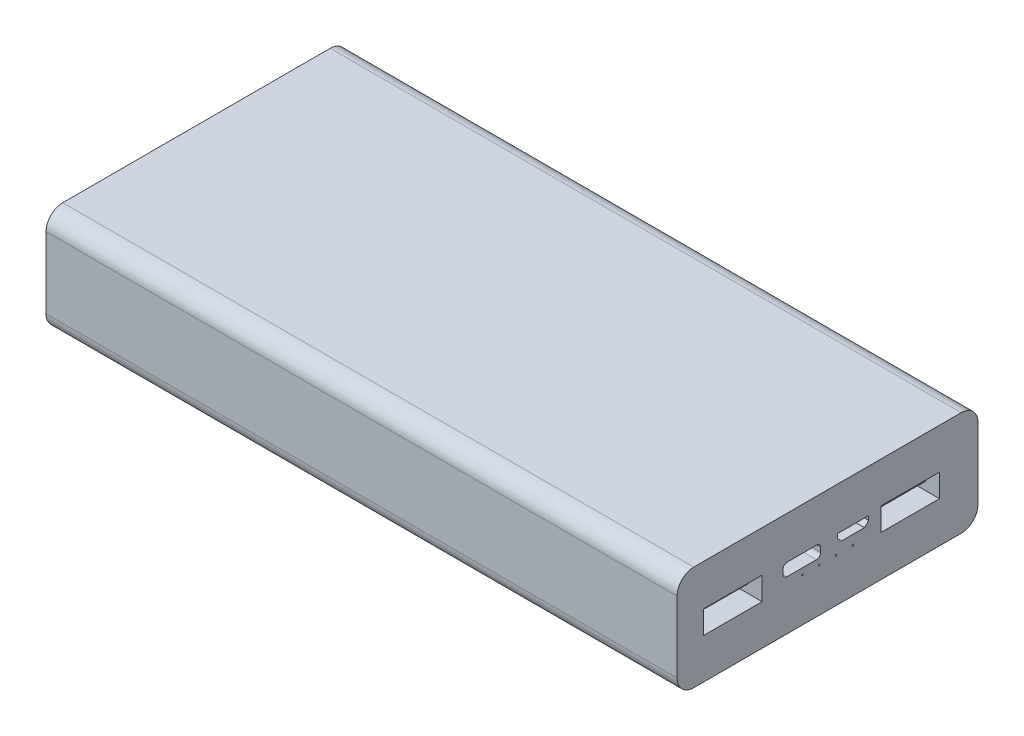
SolidWorks part; units mm, degrees
material "ABS"
ref_plane "Front" through (0, 0, 0) normal (0, 0, 1) x (1, 0, 0)
ref_plane "Top" through (0, 0, 0) normal (0, 1, 0) x (1, 0, 0)
ref_plane "Right" through (0, 0, 0) normal (1, 0, 0) x (0, 0, -1)
sketch "草图1" plane through (0, 0, 0) normal (0, 1, 0) x (1, 0, 0)
  line L1 (53.6854, -36.3817) -> (-97.3146, -36.3817)
  line L2 (53.6854, -36.3817) -> (53.6854, 35.6183)
  line L3 (53.6854, 35.6183) -> (-97.3146, 35.6183)
  line L4 (-97.3146, -36.3817) -> (-97.3146, 35.6183)
  dimension "D1" = 151
  dimension "D2" = 72
extrude "凸台-拉伸1" add sketch "草图1" along normal blind 25
fillet "圆角1" radius 4 1 edges at (-21.8146, 25, 36.3817)
fillet "圆角2" radius 4 1 edges at (-21.8146, 25, -35.6183)
fillet "圆角3" radius 4 1 edges at (-21.8146, 0, 36.3817)
fillet "圆角4" radius 4 1 edges at (-21.8146, 0, -35.6183)
sketch "草图2" plane through (53.6854, 0, 0) normal (1, 0, 0) x (0, 0, -1)
  line L0 (-0.3817, 31.1144) -> (-0.3817, -2.5055) construction
  line L1 (-30.0329, 15.1581) -> (-16.0329, 15.1581)
  line L2 (-30.0329, 15.1581) -> (-30.0329, 9.6581)
  line L3 (-30.0329, 9.6581) -> (-16.0329, 9.6581)
  line L4 (-16.0329, 15.1581) -> (-16.0329, 9.6581)
  line L5 (-10.0329, 14.8548) -> (-3.0329, 14.8548)
  line L6 (-11.0329, 13.8548) -> (-11.0329, 12.8548)
  line L7 (-10.0329, 11.8548) -> (-3.0329, 11.8548)
  line L8 (-2.0329, 13.8548) -> (-2.0329, 12.8548)
  line L9 (1.9671, 14.7412) -> (9.4671, 14.7412)
  line L10 (1.9671, 14.7412) -> (1.9671, 13.7412)
  line L11 (2.9671, 12.7412) -> (8.4671, 12.7412)
  line L12 (9.4671, 14.7412) -> (9.4671, 13.7412)
  line L13 (12.4007, 15.2772) -> (26.4007, 15.2772)
  line L14 (12.4007, 15.2772) -> (12.4007, 9.7772)
  line L15 (12.4007, 9.7772) -> (26.4007, 9.7772)
  line L16 (26.4007, 15.2772) -> (26.4007, 9.7772)
  line L17 (-36.3817, 21) -> (-36.3817, 4) construction
  line L18 (35.6183, 21) -> (35.6183, 4) construction
  line L19 (40.6915, 12.5) -> (-43.5475, 12.5) construction
  line L20 (-32.3817, 25) -> (31.6183, 25) construction
  line L21 (-32.3817, 0) -> (31.6183, 0) construction
  line L22 (1.9671, 13.7412) -> (2.9671, 12.7412)
  line L23 (9.4671, 13.7412) -> (8.4671, 12.7412)
  arc A0 (-2.0329, 12.8548) -> (-3.0329, 11.8548) centre (-3.0329, 12.8548) cw
  arc A1 (-3.0329, 14.8548) -> (-2.0329, 13.8548) centre (-3.0329, 13.8548) cw
  arc A2 (-11.0329, 12.8548) -> (-10.0329, 11.8548) centre (-10.0329, 12.8548) ccw
  arc A3 (-11.0329, 13.8548) -> (-10.0329, 14.8548) centre (-10.0329, 13.8548) cw
  circle A4 centre (-6.3817, 10.439) radius 0.2
  circle A5 centre (-2.3817, 10.439) radius 0.2
  circle A6 centre (1.6183, 10.439) radius 0.2
  circle A7 centre (5.6183, 10.439) radius 0.2
  point P32 (-2.0329, 14.8548)
  point P35 (-11.0329, 11.8548)
  point P38 (-11.0329, 14.8548)
  dimension "D8" = 1
  dimension "D10" = 4
  dimension "D1" = 14
  dimension "D2" = 5.5
  dimension "D3" = 14
  dimension "D4" = 5.5
  dimension "D5" = 9
  dimension "D6" = 3
  dimension "D7" = 5
  dimension "D9" = 7.5
  dimension "D11" = 4
  dimension "D12" = 135
  dimension "D13" = 1
  dimension "D14" = 1
  dimension "D15" = 135
  dimension "D16" = 2
extrude "切除-拉伸1" cut sketch "草图2" against normal blind 15 contours L14 L15 L16 L13 | L2 L3 L4 L1 | L7 A0 L8 A1 L5 A3 L6 A2 | L11 L23 L12 L9 L10 L22 | A4 | A5 | A6 | A7
sketch "草图3" plane through (38.6854, 0, 0) normal (1, 0, 0) x (0, 0, -1)
  line L0 (-23.0329, 18.6783) -> (-23.0329, 7.2414) construction
  line L1 (-29.2196, 14.1359) -> (-16.8463, 14.1359)
  line L2 (-29.2196, 14.1359) -> (-29.2196, 12.5535)
  line L3 (-29.2196, 12.5535) -> (-16.8463, 12.5535)
  line L4 (-16.8463, 14.1359) -> (-16.8463, 12.5535)
  line L5 (13.2141, 14.1359) -> (25.5873, 14.1359)
  line L6 (13.2141, 14.1359) -> (13.2141, 12.5535)
  line L7 (13.2141, 12.5535) -> (25.5873, 12.5535)
  line L8 (25.5873, 14.1359) -> (25.5873, 12.5535)
  line L9 (19.4007, 18.6783) -> (19.4007, 6.637) construction
  line L10 (-16.0329, 15.1581) -> (-16.0329, 9.6581) construction
  line L12 (-30.0329, 15.1581) -> (-30.0329, 9.6581) construction
  line L13 (26.4007, 15.2772) -> (26.4007, 9.7772) construction
  line L14 (12.4007, 15.2772) -> (12.4007, 9.7772) construction
  line L15 (-6.5329, 15.8891) -> (-6.5329, 11.4136) construction
  line L16 (-10.0717, 13.4486) -> (-2.9942, 13.4486)
  line L17 (-10.0717, 13.4486) -> (-10.0717, 12.9486)
  line L18 (-10.0717, 12.9486) -> (-2.9942, 12.9486)
  line L19 (-2.9942, 13.4486) -> (-2.9942, 12.9486)
  line L20 (3.8127, 14.013) -> (7.6214, 14.013)
  line L21 (3.8127, 14.013) -> (3.8127, 13.813)
  line L22 (3.8127, 13.813) -> (7.6214, 13.813)
  line L23 (7.6214, 14.013) -> (7.6214, 13.813)
  line L24 (-11.0329, 13.8548) -> (-11.0329, 12.8548) construction
  line L25 (-2.0329, 13.8548) -> (-2.0329, 12.8548) construction
  line L26 (5.7171, 15.4512) -> (5.7171, 11.9019) construction
  line L27 (1.9671, 14.7412) -> (1.9671, 13.7412) construction
  line L28 (9.4671, 14.7412) -> (9.4671, 13.7412) construction
  dimension "D1" = 0.5
  dimension "D2" = 0.2
extrude "凸台-拉伸2" add sketch "草图3" along normal blind 13
chamfer "倒角1" distance 0.5 angle 45 1 edges at (51.6854, 12.5535, 23.0329)
chamfer "倒角2" distance 0.5 angle 45 1 edges at (51.6854, 14.1359, 23.0329)
chamfer "倒角3" distance 0.5 angle 45 1 edges at (51.6854, 13.3447, 29.2196)
chamfer "倒角4" distance 0.5 angle 45 1 edges at (51.6854, 13.3447, 16.8463)
chamfer "倒角5" distance 0.5 angle 45 4 edges at (51.6854, 13.3447, -13.2141) (51.6854, 14.1359, -19.4007) (51.6854, 13.3447, -25.5873) (51.6854, 12.5535, -19.4007)
sketch "草图4" plane through (0, 0, -35.6183) normal (0, 0, -1) x (-1, 0, 0)
  line L0 (-53.6854, 21) -> (-53.6854, 4) construction
  line L1 (-40.8854, 14.2739) -> (-30.4854, 14.2739)
  line L2 (-41.6854, 13.4739) -> (-41.6854, 10.3788)
  line L3 (-40.8854, 9.5788) -> (-30.4854, 9.5788)
  line L4 (-29.6854, 13.4739) -> (-29.6854, 10.3788)
  line L6 (-40.8854, 14.3239) -> (-30.4854, 14.3239)
  line L7 (-41.7354, 13.4739) -> (-41.7354, 10.3788)
  line L8 (-40.8854, 9.5288) -> (-30.4854, 9.5288)
  line L9 (-29.6354, 13.4739) -> (-29.6354, 10.3788)
  arc A0 (-30.4854, 14.2739) -> (-29.6854, 13.4739) centre (-30.4854, 13.4739) cw
  arc A1 (-30.4854, 9.5788) -> (-29.6854, 10.3788) centre (-30.4854, 10.3788) ccw
  arc A2 (-40.8854, 9.5788) -> (-41.6854, 10.3788) centre (-40.8854, 10.3788) cw
  arc A3 (-41.6854, 13.4739) -> (-40.8854, 14.2739) centre (-40.8854, 13.4739) cw
  arc A4 (-30.4854, 9.5288) -> (-29.6354, 10.3788) centre (-30.4854, 10.3788) ccw
  arc A5 (-29.6354, 13.4739) -> (-30.4854, 14.3239) centre (-30.4854, 13.4739) ccw
  arc A6 (-41.7354, 10.3788) -> (-40.8854, 9.5288) centre (-40.8854, 10.3788) ccw
  arc A7 (-41.7354, 13.4739) -> (-40.8854, 14.3239) centre (-40.8854, 13.4739) cw
  dimension "D1" = 0.8
  dimension "D2" = 0.8
  dimension "D10" = 0.85
  dimension "D3" = 12
  dimension "D4" = 4.6951
  dimension "D5" = 12
  dimension "D6" = 0.05
  dimension "D7" = 0.05
  dimension "D8" = 0.05
  dimension "D9" = 0.05
extrude "切除-拉伸2" cut sketch "草图4" against normal blind 3
sketch "草图5" plane through (0, 0, -35.6183) normal (0, 0, -1) x (-1, 0, 0)
  line L0 (-30.4854, 14.3239) -> (-40.8854, 14.3239) construction
  line L1 (-40.9354, 14.8239) -> (-30.4354, 14.8239)
  line L2 (-42.2354, 13.5239) -> (-42.2354, 10.3288)
  line L3 (-40.9354, 9.0288) -> (-30.4354, 9.0288)
  line L4 (-29.1354, 13.5239) -> (-29.1354, 10.3288)
  line L5 (-29.6354, 10.3788) -> (-29.6354, 13.4739) construction
  line L6 (-40.8854, 9.5288) -> (-30.4854, 9.5288) construction
  line L7 (-41.7354, 13.4739) -> (-41.7354, 10.3788) construction
  arc A0 (-40.9354, 9.0288) -> (-42.2354, 10.3288) centre (-40.9354, 10.3288) cw
  arc A1 (-30.4354, 9.0288) -> (-29.1354, 10.3288) centre (-30.4354, 10.3288) ccw
  arc A2 (-30.4354, 14.8239) -> (-29.1354, 13.5239) centre (-30.4354, 13.5239) cw
  arc A3 (-40.9354, 14.8239) -> (-42.2354, 13.5239) centre (-40.9354, 13.5239) ccw
  dimension "D5" = 1.3
  dimension "D1" = 0.5
  dimension "D2" = 0.5
  dimension "D3" = 0.5
  dimension "D4" = 0.5
ref_plane "基准面1" through (0, 11, 0) normal (0, 1, 0) x (1, 0, 0)
sketch "草图6" plane through (0, 11, 0) normal (0, 1, 0) x (1, 0, 0)
  line L1 (41.7354, 35.5168) -> (41.7354, 35.6183)
  line L2 (41.7354, 35.6183) -> (42.2354, 35.6183)
  line L3 (30.4854, 35.6183) -> (29.6354, 35.6183) construction
  line L4 (42.2354, 35.6183) -> (42.1849, 35.5157) construction
  line L5 (42.1849, 35.5157) -> (41.7354, 35.5168) construction
  spline S0 degree 2 poles (42.2354, 35.6183) (42.1849, 35.5157) (41.7354, 35.5168) knots 0 0 0 1 1 1
sweep "切除-扫描1" cut profiles "草图6" path "草图5"
